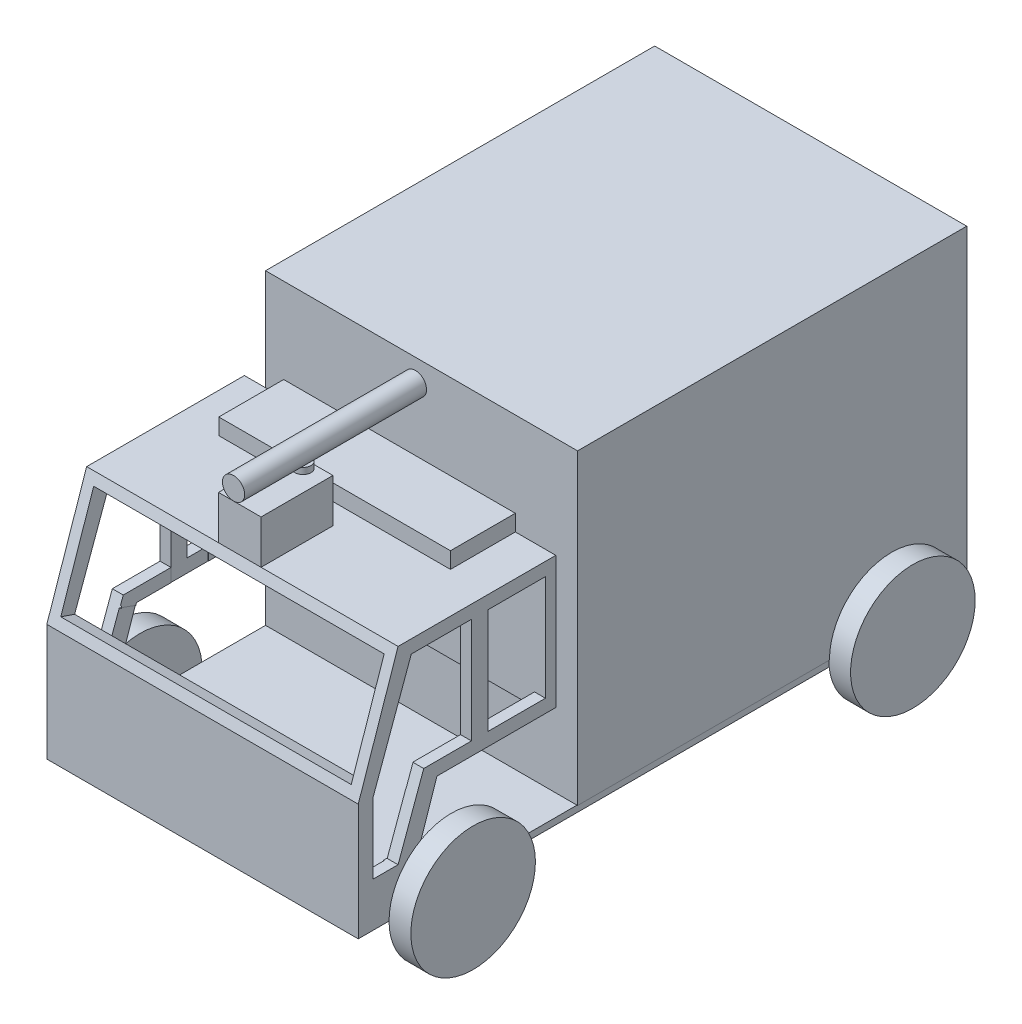
SolidWorks part; units mm, degrees
ref_plane "Front Plane" through (0, 0, 0) normal (0, 0, 1) x (1, 0, 0)
ref_plane "Top Plane" through (0, 0, 0) normal (0, 1, 0) x (1, 0, 0)
ref_plane "Right Plane" through (0, 0, 0) normal (1, 0, 0) x (0, 0, -1)
sketch "Çizim2" plane through (0, 0, 0) normal (1, 0, 0) x (0, 0, -1)
  line L0 (309.0115, 611.5197) -> (1226.0739, 683.2855) construction
  line L6 (1257.8367, 931.4533) -> (633.0024, 931.4533)
  line L7 (1257.8367, 931.4533) -> (1257.8367, 438.3349)
  line L8 (1257.8367, 438.3349) -> (633.0024, 438.3349)
  line L9 (633.0024, 931.4533) -> (633.0024, 438.3349)
extrude "Yükseklik-Ekstrüzyon1" add sketch "Çizim2" against normal blind 500
sketch "Çizim4" plane through (0, 0, 0) normal (1, 0, 0) x (0, 0, -1)
  line L0 (633.0024, 438.3349) -> (1257.8367, 438.3349) construction
  circle A0 centre (1137.3543, 438.3349) radius 100
extrude "Yükseklik-Ekstrüzyon2" add sketch "Çizim4" along normal blind 35
sketch "Çizim5" plane through (0, 0, 0) normal (1, 0, 0) x (0, 0, -1)
  line L1 (1257.8367, 438.3349) -> (281.8689, 438.3349)
  line L2 (1257.8367, 438.3349) -> (1257.8367, 427.9396)
  line L3 (1257.8367, 427.9396) -> (281.8689, 427.9396)
  line L4 (281.8689, 438.3349) -> (281.8689, 427.9396)
extrude "Yükseklik-Ekstrüzyon3" add sketch "Çizim5" against normal blind 500
sketch "Çizim6" plane through (0, 0, 0) normal (1, 0, 0) x (0, 0, -1)
  line L1 (281.8689, 427.9396) -> (599.0713, 427.9396)
  line L2 (281.8689, 427.9396) -> (281.8689, 802.644)
  line L3 (281.8689, 802.644) -> (599.0713, 802.644)
  line L4 (599.0713, 427.9396) -> (599.0713, 802.644)
extrude "Yükseklik-Ekstrüzyon4" add sketch "Çizim6" against normal blind 500
sketch "Çizim7" plane through (0, 0, 0) normal (1, 0, 0) x (0, 0, -1)
  line L0 (281.8689, 802.644) -> (345.8192, 802.644)
  line L1 (599.0713, 802.644) -> (281.8689, 802.644) construction
  line L2 (345.8192, 802.644) -> (281.8689, 615.2918)
  line L3 (281.8689, 802.644) -> (281.8689, 427.9396) construction
  line L4 (281.8689, 615.2918) -> (281.8689, 802.644)
extrude "Kes-Ekstrüzyon1" cut sketch "Çizim7" against normal blind 500
sketch "Çizim8" plane through (0, 0, 0) normal (1, 0, 0) x (0, 0, -1)
  line L0 (345.8192, 802.644) -> (367.0324, 781.4308) construction
  line L1 (367.0324, 781.4308) -> (305.4688, 612.2862)
  line L2 (305.4688, 612.2862) -> (305.4688, 499.1233)
  line L3 (305.4688, 499.1233) -> (345.8192, 499.1233)
  line L4 (345.8192, 499.1233) -> (387.0072, 612.2862)
  line L5 (387.0072, 612.2862) -> (582.3923, 612.2862)
  line L6 (582.3923, 612.2862) -> (582.3923, 781.4308)
  line L7 (582.3923, 781.4308) -> (367.0324, 781.4308)
extrude "Kes-Ekstrüzyon2" cut sketch "Çizim8" against normal blind 500
sketch "Çizim10" plane through (0, 0, 0) normal (1, 0, 0) x (0, 0, -1)
  line L0 (387.0072, 612.2862) -> (408.2204, 591.0729) construction
  line L1 (599.0713, 438.3349) -> (356.5412, 438.3349)
  line L2 (356.5412, 438.3349) -> (408.2204, 591.0729)
  line L3 (408.2204, 591.0729) -> (599.0713, 591.0729)
  line L4 (599.0713, 438.3349) -> (599.0713, 802.644) construction
  line L5 (599.0713, 591.0729) -> (599.0713, 438.3349)
extrude "Kes-Ekstrüzyon3" cut sketch "Çizim10" against normal blind 500
sketch "Çizim11" plane through (0, 0, 0) normal (1, 0, 0) x (0, 0, -1)
  line L0 (281.8689, 427.9396) -> (1037.8961, 427.9396) construction
  circle A0 centre (431.3213, 427.9396) radius 100
extrude "Yükseklik-Ekstrüzyon5" add sketch "Çizim11" along normal blind 35
sketch "Çizim12" plane through (0, -21.9648, -64.3494) normal (0, 0.323, 0.9464) x (1, 0, 0)
  line L0 (-500, 871.3238) -> (0, 673.3578) construction
  line L6 (-483.1517, 690.3914) -> (-16.8483, 690.3914)
  line L7 (-483.1517, 690.3914) -> (-483.1517, 854.2902)
  line L8 (-483.1517, 854.2902) -> (-16.8483, 854.2902)
  line L9 (-16.8483, 690.3914) -> (-16.8483, 854.2902)
  line L10 (-483.1517, 690.3914) -> (-16.8483, 854.2902) construction
  line L11 (-483.1517, 854.2902) -> (-16.8483, 690.3914) construction
  point P2 (-250, 772.3408)
extrude "Kes-Ekstrüzyon4" cut sketch "Çizim12" against normal blind 35
sketch "Çizim15" plane through (0, 802.644, 0) normal (0, 1, 0) x (1, 0, 0)
  line L1 (-500, 582.3923) -> (0, 582.3923)
  line L2 (-500, 582.3923) -> (-500, 382.565)
  line L3 (-500, 382.565) -> (0, 382.565)
  line L4 (0, 582.3923) -> (0, 382.565)
sketch "Çizim17" plane through (0, 612.2862, 0) normal (0, 1, 0) x (1, 0, 0)
  line L0 (-500, 582.3923) -> (0, 382.565) construction
  line L1 (-500, 582.3923) -> (0, 582.3923) construction
  line L2 (-482.4354, 382.565) -> (-17.5646, 382.565)
  line L3 (-482.4354, 382.565) -> (-482.4354, 582.3923)
  line L4 (-482.4354, 582.3923) -> (-17.5646, 582.3923)
  line L5 (-17.5646, 382.565) -> (-17.5646, 582.3923)
  line L6 (-482.4354, 382.565) -> (-17.5646, 582.3923) construction
  line L7 (-482.4354, 582.3923) -> (-17.5646, 382.565) construction
  point P4 (-250, 482.4786)
extrude "Kes-Ekstrüzyon7" cut sketch "Çizim17" against normal blind 35
sketch "Çizim20" plane through (0, -52.7578, -144.9509) normal (0, 0.342, 0.9397) x (1, 0, 0)
  line L1 (-483.1517, 691.6201) -> (-17.4913, 691.6201)
  line L2 (-483.1517, 691.6201) -> (-483.1517, 587.0287)
  line L3 (-483.1517, 587.0287) -> (-17.4913, 587.0287)
  line L4 (-17.4913, 691.6201) -> (-17.4913, 587.0287)
extrude "Kes-Ekstrüzyon8" cut sketch "Çizim20" against normal blind 35
sketch "Çizim21" plane through (0, -52.7578, -144.9509) normal (0, 0.342, 0.9397) x (1, 0, 0)
  line L0 (-500, 674.59) -> (0, 674.59) construction
  line L1 (-480.7848, 707.7483) -> (-17.2215, 707.7483)
  line L2 (-480.7848, 707.7483) -> (-480.7848, 674.59)
  line L3 (-480.7848, 674.59) -> (-17.2215, 674.59)
  line L4 (-17.2215, 707.7483) -> (-17.2215, 674.59)
extrude "Kes-Ekstrüzyon9" cut sketch "Çizim21" against normal blind 35
sketch "Çizim22" plane through (0, -63.2177, -186.8402) normal (0, -0.3205, -0.9472) x (-1, 0, 0)
  line L1 (17.9505, 583.6669) -> (483.7207, 583.6669)
  line L2 (17.9505, 583.6669) -> (17.9505, 527.9641)
  line L3 (17.9505, 527.9641) -> (483.7207, 527.9641)
  line L4 (483.7207, 583.6669) -> (483.7207, 527.9641)
extrude "Kes-Ekstrüzyon10" cut sketch "Çizim22" against normal blind 35
sketch "Çizim23" plane through (0, 499.1233, 0) normal (0, 1, 0) x (1, 0, 0)
  line L1 (-483.1517, 340.3168) -> (-16.8483, 340.3168)
  line L2 (-483.1517, 340.3168) -> (-483.1517, 309.6609)
  line L3 (-483.1517, 309.6609) -> (-16.8483, 309.6609)
  line L4 (-16.8483, 340.3168) -> (-16.8483, 309.6609)
extrude "Kes-Ekstrüzyon11" cut sketch "Çizim23" against normal blind 60
sketch "Çizim25" plane through (0, 0, 0) normal (1, 0, 0) x (0, 0, -1)
  line L0 (582.3923, 802.644) -> (382.565, 802.644) construction
  line L1 (463.6587, 802.644) -> (489.9327, 802.644)
  line L2 (463.6587, 802.644) -> (463.6587, 591.0729)
  line L3 (463.6587, 591.0729) -> (489.9327, 591.0729)
  line L4 (489.9327, 802.644) -> (489.9327, 591.0729)
  line L5 (599.0713, 591.0729) -> (408.2204, 591.0729) construction
extrude "Yükseklik-Ekstrüzyon6" add sketch "Çizim25" against normal blind 500
sketch "Çizim27" plane through (0, 0, -463.6587) normal (0, 0, 1) x (1, 0, 0)
  line L0 (-500, 708.9679) -> (-482.78, 708.9679) construction
  line L1 (-500, 615.2918) -> (-500, 802.644) construction
  line L2 (0, 702.4781) -> (-16.8483, 702.4781) construction
  line L3 (0, 615.2918) -> (0, 802.644) construction
  line L4 (-16.8483, 631.4122) -> (-16.8483, 786.5237) construction
  line L5 (-500, 781.4308) -> (0, 781.4308) construction
  line L6 (-482.78, 781.4308) -> (-17.5646, 781.4308)
  line L7 (-482.78, 781.4308) -> (-482.78, 591.0729)
  line L8 (-482.78, 591.0729) -> (-17.5646, 591.0729)
  line L9 (-17.5646, 781.4308) -> (-17.5646, 591.0729)
extrude "Kes-Ekstrüzyon12" cut sketch "Çizim27" against normal blind 60
sketch "Çizim28" plane through (-500, 0, 0) normal (-1, 0, 0) x (0, 0, 1)
  line L0 (-531.3213, 427.9396) -> (-331.3213, 427.9396) construction
  line L1 (-633.0024, 438.3349) -> (-1257.8367, 438.3349) construction
  line L2 (-1257.8367, 427.9396) -> (-1257.8367, 931.4533) construction
  line L3 (-1236.8125, 427.9396) -> (-1034.6148, 438.3349) construction
  line L4 (-1135.7136, 433.1372) -> (-1135.7136, 438.3349) construction
  circle A0 centre (-431.3213, 427.9396) radius 100
  circle A1 centre (-1135.7136, 438.3349) radius 100
extrude "Yükseklik-Ekstrüzyon7" add sketch "Çizim28" along normal blind 35
sketch "Çizim46" plane through (0, 802.644, 0) normal (0, 1, 0) x (1, 0, 0)
  line L0 (-500, 345.8192) -> (0, 345.8192) construction
  line L1 (-220, 461.2215) -> (-288.2902, 461.2215)
  line L2 (-220, 461.2215) -> (-220, 345.8192)
  line L3 (-220, 345.8192) -> (-288.2902, 345.8192)
  line L4 (-288.2902, 461.2215) -> (-288.2902, 345.8192)
extrude "Yükseklik-Ekstrüzyon14" add sketch "Çizim46" along normal blind 70
sketch "Çizim47" plane through (0, 872.644, 0) normal (0, 1, 0) x (1, 0, 0)
  circle A0 centre (-254.1451, 447.3584) radius 12.7126
extrude "Yükseklik-Ekstrüzyon15" add sketch "Çizim47" along normal blind 10
sketch "Çizim48" plane through (0, 0, -345.8192) normal (0, 0, 1) x (1, 0, 0)
  circle A0 centre (-254.1451, 900.4528) radius 17.8087
extrude "Yükseklik-Ekstrüzyon18" add sketch "Çizim48" along normal blind 10 and the other way blind 282 separate body
sketch "Çizim49" plane through (0, 802.644, 0) normal (0, 1, 0) x (1, 0, 0)
  line L0 (-500, 599.0713) -> (0, 599.0713) construction
  line L1 (-436.9361, 494.9063) -> (-65.0108, 494.9063)
  line L2 (-436.9361, 494.9063) -> (-436.9361, 599.0713)
  line L3 (-436.9361, 599.0713) -> (-65.0108, 599.0713)
  line L4 (-65.0108, 494.9063) -> (-65.0108, 599.0713)
  line L5 (-436.9361, 494.9063) -> (-65.0108, 599.0713) construction
  line L6 (-436.9361, 599.0713) -> (-65.0108, 494.9063) construction
  point P0 (-250.9734, 546.9888)
extrude "Yükseklik-Ekstrüzyon19" add sketch "Çizim49" along normal blind 26
sketch "Çizim54" plane through (0, 0, 0) normal (1, 0, 0) x (0, 0, -1)
  line L1 (1257.8367, 931.4533) -> (633.0024, 931.4533)
  line L2 (1257.8367, 931.4533) -> (1257.8367, 438.3349)
  line L3 (1257.8367, 438.3349) -> (633.0024, 438.3349)
  line L4 (633.0024, 931.4533) -> (633.0024, 438.3349)
extrude "Yükseklik-Ekstrüzyon20" add sketch "Çizim54" along normal blind 1
